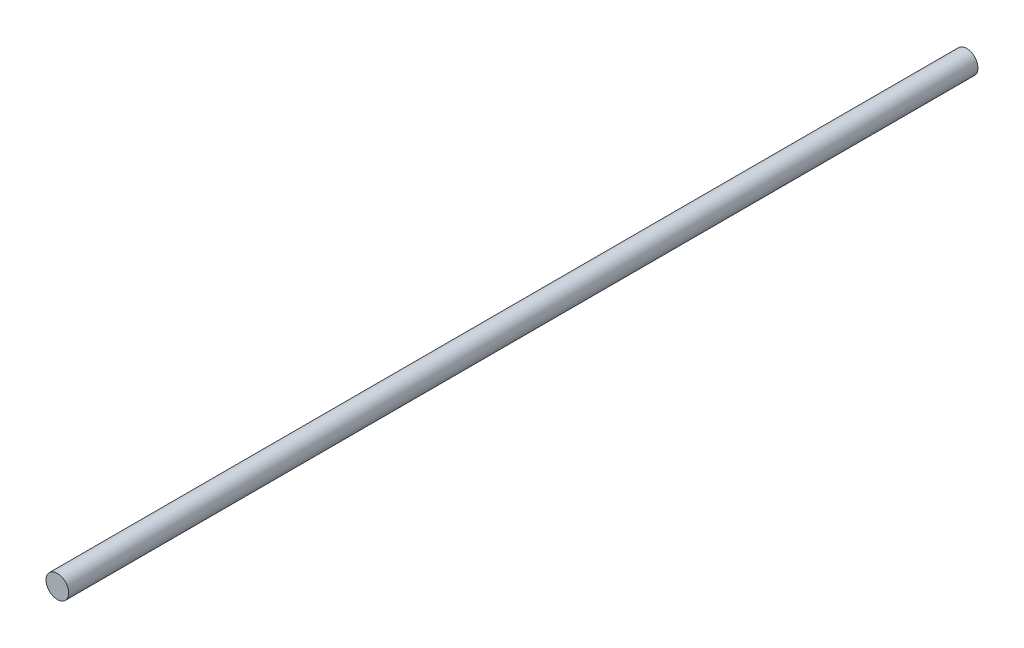
SolidWorks part; units mm, degrees
ref_plane "前基準面" through (0, 0, 0) normal (0, 0, 1) x (1, 0, 0)
ref_plane "上基準面" through (0, 0, 0) normal (0, 1, 0) x (1, 0, 0)
ref_plane "右基準面" through (0, 0, 0) normal (1, 0, 0) x (0, 0, -1)
sketch "草圖1" plane through (0, 0, 0) normal (0, 0, 1) x (1, 0, 0)
  circle A0 centre (0, 0) radius 1.25
extrude "填料-伸長1" add sketch "草圖1" along normal blind 100
